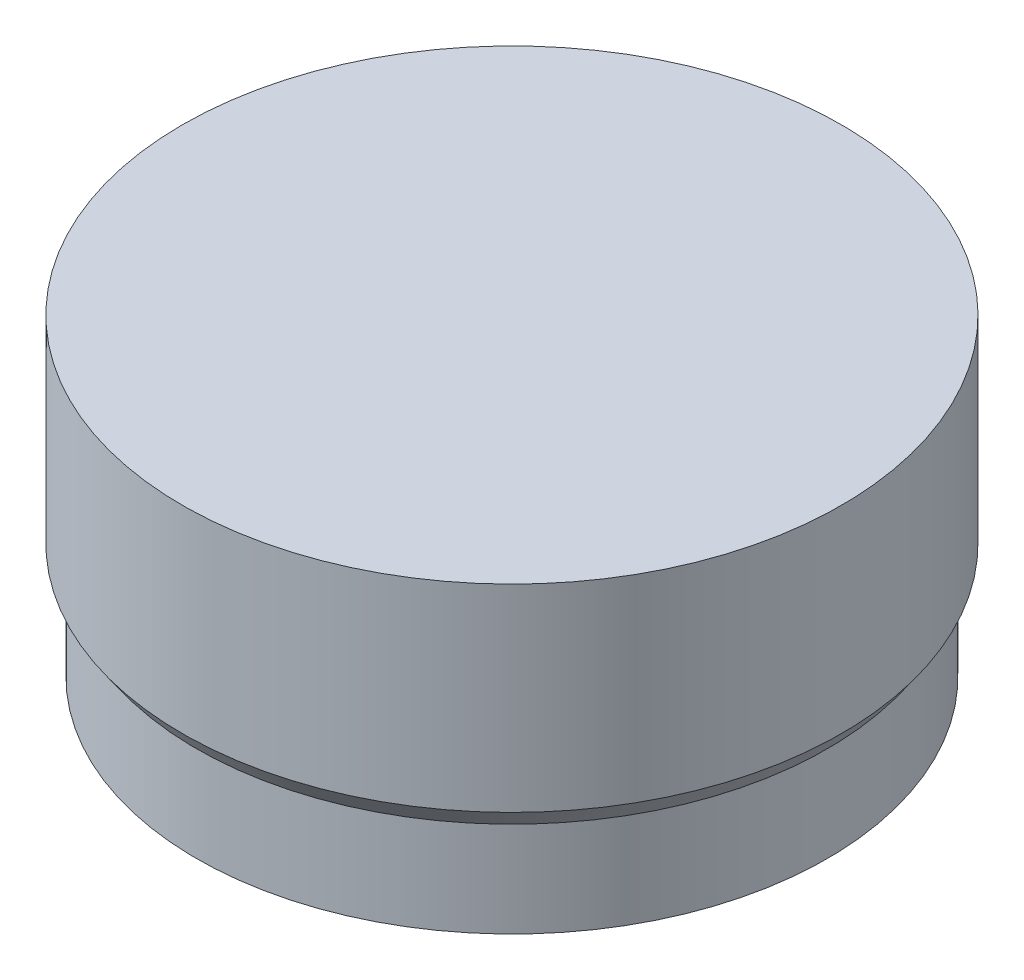
SolidWorks part; units mm, degrees
ref_plane "Front Plane" through (0, 0, 0) normal (0, 0, 1) x (1, 0, 0)
ref_plane "Top Plane" through (0, 0, 0) normal (0, 1, 0) x (1, 0, 0)
ref_plane "Right Plane" through (0, 0, 0) normal (1, 0, 0) x (0, 0, -1)
sketch "Sketch1" plane through (0, 0, 0) normal (0, 0, 1) x (1, 0, 0)
  line L0 (0, 0) -> (1.7207, 2.4575)
  line L1 (1.7207, 2.4575) -> (1.7207, 26.4575)
  line L2 (1.7207, 26.4575) -> (-0.6793, 26.4575)
  line L6 (1.7207, 2.4575) -> (1.7207, -1.7935) construction
  line L7 (-38.2793, 29.419) -> (-38.2793, -8.433) construction
  line L8 (-0.6793, 26.4575) -> (-38.2793, 26.4575)
  line L9 (-38.2793, 26.4575) -> (-38.2793, -11.5425)
  line L10 (-38.2793, -11.5425) -> (0, -11.5425)
  line L11 (0, -11.5425) -> (0, 0)
  dimension "D1" = 24
  dimension "D2" = 35
  dimension "D3" = 40
  dimension "D4" = 3
  dimension "D5" = 38
revolve "Revolve1" add sketch "Sketch1" angle 360 about L7
